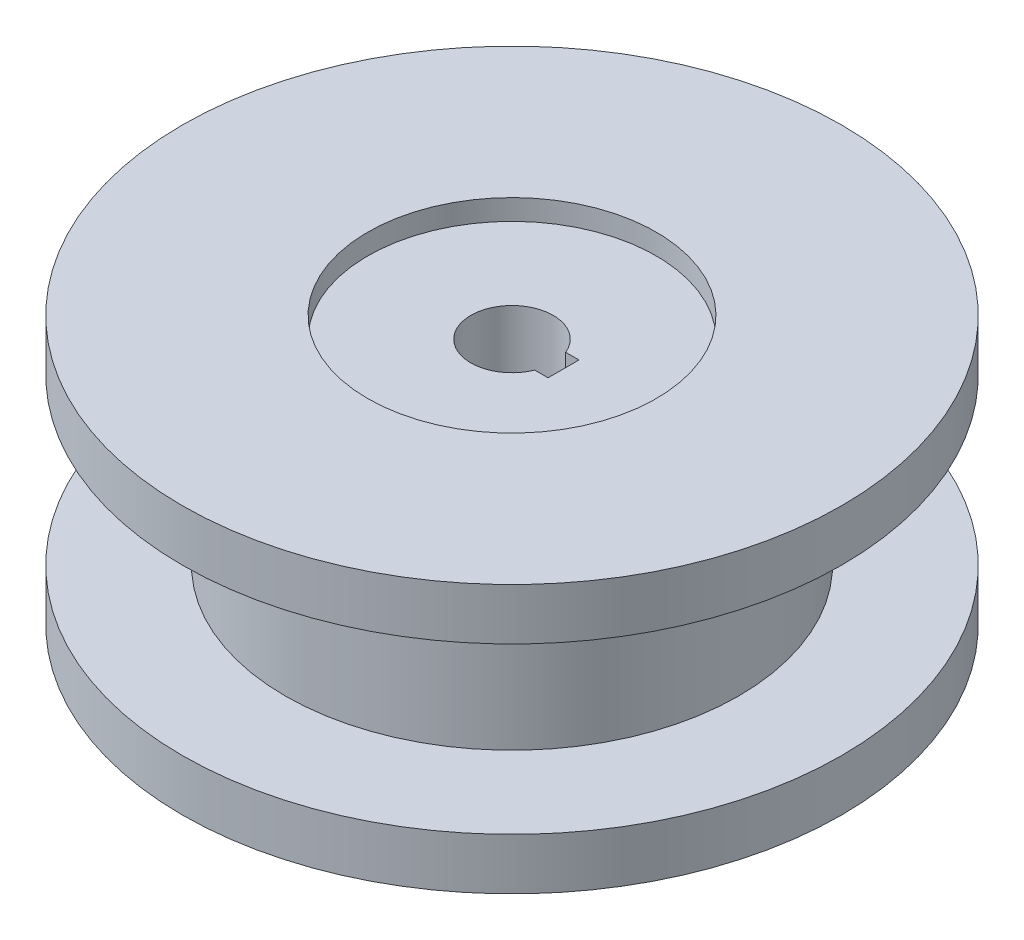
SolidWorks part; units mm, degrees
ref_plane "Front Plane" through (0, 0, 0) normal (0, 0, 1) x (1, 0, 0)
ref_plane "Top Plane" through (0, 0, 0) normal (0, 1, 0) x (1, 0, 0)
ref_plane "Right Plane" through (0, 0, 0) normal (1, 0, 0) x (0, 0, -1)
sketch "Sketch1" plane through (0, 0, 0) normal (0, 0, 1) x (1, 0, 0)
  line L0 (0, 93.8108) -> (0, -87.4865) construction
  line L1 (-111.7297, 0) -> (104.3514, 0) construction
  line L2 (0, 65) -> (160, 65)
  line L3 (160, 65) -> (160, 40)
  line L4 (160, 40) -> (110, 40)
  line L5 (110, 40) -> (110, -40)
  line L6 (160, -40) -> (110, -40)
  line L7 (160, -65) -> (160, -40)
  line L8 (0, -65) -> (160, -65)
  line L9 (0, 65) -> (0, -65)
  point P11 (110, 0)
  dimension "D1" = 130
  dimension "D2" = 25
  dimension "D3" = 160
  dimension "D4" = 110
revolve "Revolve1" add sketch "Sketch1" angle 360 about L0
sketch "Sketch2" plane through (0, 65, 0) normal (0, 1, 0) x (1, 0, 0)
  circle A0 centre (0, 0) radius 70
  dimension "D1" = 140
extrude "Cut-Extrude1" cut sketch "Sketch2" against normal blind 10
mirror "Mirror1" about plane through (0, 0, 0) normal (0, 1, 0) of "Cut-Extrude1"
sketch "Sketch3" plane through (0, 55, 0) normal (0, 1, 0) x (1, 0, 0)
  circle A0 centre (0, 0) radius 20
  dimension "D1" = 40
extrude "Cut-Extrude2" cut sketch "Sketch3" against normal through all
sketch "Sketch4" plane through (0, 55, 0) normal (0, 1, 0) x (1, 0, 0)
  line L0 (185.4919, 0) -> (0, 0) construction
  line L2 (5.5451, -7.5) -> (25, -7.5)
  line L3 (5.5451, -7.5) -> (5.5451, 7.5)
  line L4 (5.5451, 7.5) -> (25, 7.5)
  line L5 (25, -7.5) -> (25, 7.5)
  line L6 (5.5451, -7.5) -> (25, 7.5) construction
  line L7 (5.5451, 7.5) -> (25, -7.5) construction
  point P3 (15.2725, 0)
  dimension "D1" = 15
  dimension "D2" = 25
extrude "Cut-Extrude3" cut sketch "Sketch4" against normal through all
